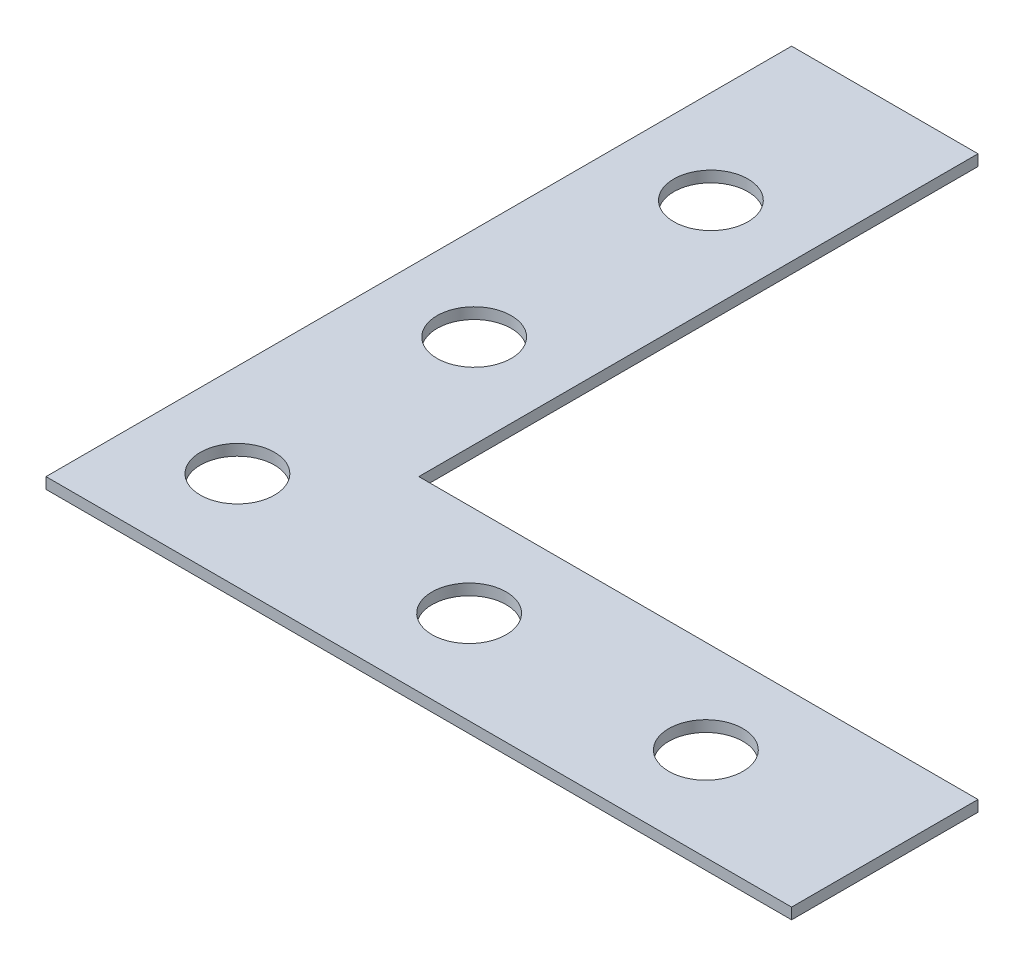
SolidWorks part; units mm, degrees
ref_plane "Front Plane" through (0, 0, 0) normal (0, 0, 1) x (1, 0, 0)
ref_plane "Top Plane" through (0, 0, 0) normal (0, 1, 0) x (1, 0, 0)
ref_plane "Right Plane" through (0, 0, 0) normal (1, 0, 0) x (0, 0, -1)
sketch "Sketch1" plane through (0, 0, 0) normal (0, 1, 0) x (1, 0, 0)
  line L0 (0, 0) -> (80, 0)
  line L3 (0, 80) -> (20, 80)
  line L4 (20, 20) -> (20, 80)
  line L7 (20, 20) -> (80, 20)
  line L8 (80, 0) -> (80, 20)
  line L9 (0, 80) -> (0, 0)
  dimension "D1" = 20
  dimension "D2" = 20
  dimension "D3" = 60
  dimension "D4" = 60
extrude "Boss-Extrude1" add sketch "Sketch1" along normal blind 1.19 contours L9 L0 L8 L7 L4 L3
sketch "Sketch2" plane through (0, 1.19, 0) normal (0, 1, 0) x (1, 0, 0)
  line L2 (0, 0) -> (80, 0) construction
  line L3 (0, 80) -> (0, 0) construction
  line L6 (20, 20) -> (80, 20) construction
  circle A0 centre (10, 61.34) radius 3.9788
  circle A1 centre (10, 35.94) radius 3.98
  circle A2 centre (10, 10.54) radius 3.98
  circle A4 centre (35.4, 10) radius 3.98
  circle A5 centre (60.8, 10) radius 3.98
  point P12 (0, 0)
  point P14 (0, 0)
  point P15 (0, 0)
  point P16 (0, 0)
  dimension "D1" = 7.9575
  dimension "D4" = 7.96
  dimension "D5" = 7.96
  dimension "D6" = 10
  dimension "D7" = 7.96
  dimension "D8" = 7.96
  dimension "D11" = 25.4
  dimension "D12" = 10.54
  dimension "D13" = 25.4
  dimension "D2" = 25.4
  dimension "D3" = 10
  dimension "D9" = 25.4
  dimension "D10" = 10
  dimension "D14" = 10
  dimension "D15" = 10
extrude "Cut-Extrude1" cut sketch "Sketch2" against normal blind 1.19
